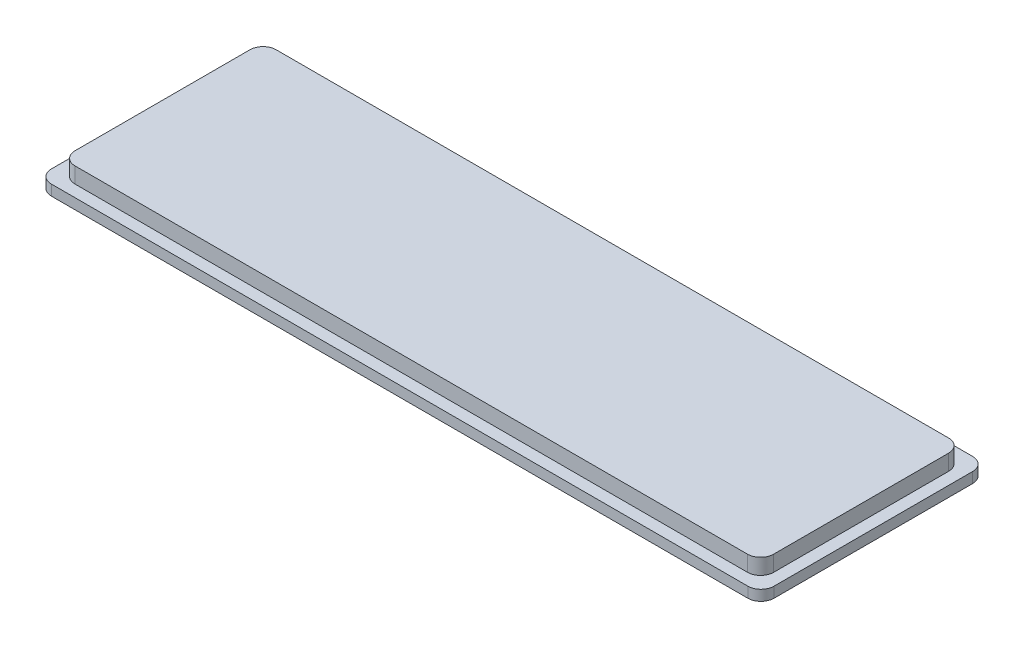
SolidWorks part; units mm, degrees
ref_plane "Front Plane" through (0, 0, 0) normal (0, 0, 1) x (1, 0, 0)
ref_plane "Top Plane" through (0, 0, 0) normal (0, 1, 0) x (1, 0, 0)
ref_plane "Right Plane" through (0, 0, 0) normal (1, 0, 0) x (0, 0, -1)
sketch "Sketch2" plane through (0, 0, 0) normal (0, 1, 0) x (1, 0, 0)
  line L1 (0, 0) -> (69.9872, 0)
  line L2 (0, 0) -> (0, 21.7678)
  line L3 (0, 21.7678) -> (69.9872, 21.7678)
  line L4 (69.9872, 0) -> (69.9872, 21.7678)
  dimension "D1" = 21.7678
  dimension "D2" = 69.9872
extrude "Boss-Extrude1" add sketch "Sketch2" along normal blind 1.016
sketch "Sketch3" plane through (0, 1.016, 0) normal (0, 1, 0) x (1, 0, 0)
  line L1 (1.143, 1.143) -> (68.8086, 1.143)
  line L2 (1.143, 1.143) -> (1.143, 20.6248)
  line L3 (1.143, 20.6248) -> (68.8086, 20.6248)
  line L4 (68.8086, 1.143) -> (68.8086, 20.6248)
  line L5 (0, 0) -> (69.9872, 0) construction
  line L6 (0, 21.7678) -> (0, 0) construction
  dimension "D1" = 67.6656
  dimension "D2" = 19.4818
  dimension "D3" = 1.143
  dimension "D4" = 1.143
extrude "Boss-Extrude2" add sketch "Sketch3" along normal blind 1.524
fillet "Fillet1" radius 1.27 8 edges at (0, 0.508, -21.7678) (1.143, 1.778, -20.6248) (0, 0.508, 0) (1.143, 1.778, -1.143) (69.9872, 0.508, -21.7678) (68.8086, 1.778, -20.6248) (68.8086, 1.778, -1.143) (69.9872, 0.508, 0)
